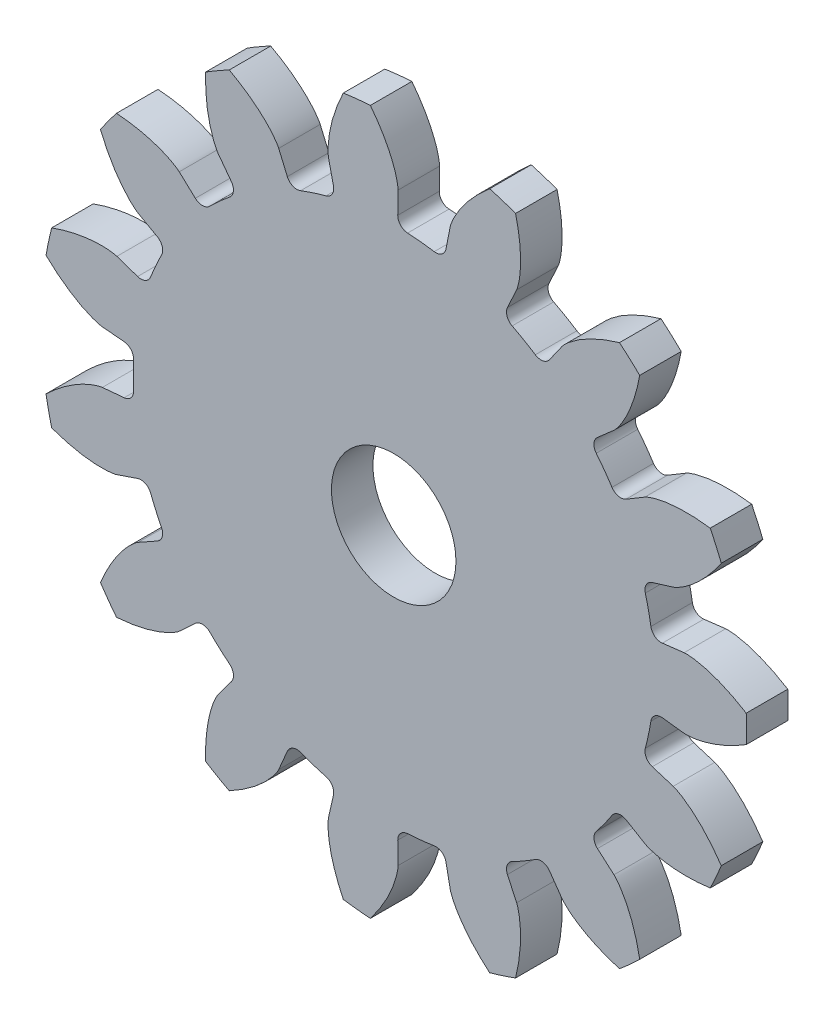
SolidWorks part; units mm, degrees
ref_plane "Front Plane" through (0, 0, 0) normal (0, 0, 1) x (1, 0, 0)
ref_plane "Top Plane" through (0, 0, 0) normal (0, 1, 0) x (1, 0, 0)
ref_plane "Right Plane" through (0, 0, 0) normal (1, 0, 0) x (0, 0, -1)
sketch "Model" plane through (0, 0, 0) normal (0, 0, 1) x (1, 0, 0)
  line L0 (-40.3391, -19.555) -> (-39.3393, -19.2145)
  line L1 (-38.3886, -21.3499) -> (-39.3106, -21.865)
  line L2 (-37.3332, -24.5867) -> (-36.5584, -23.869)
  line L3 (-39.9867, -16.1687) -> (-41.0386, -16.2643)
  line L4 (-14.0541, -16.5569) -> (-13.0053, -16.6821)
  line L5 (-16.3857, -24.2745) -> (-17.1805, -23.5789)
  line L6 (-26.7899, -29.0938) -> (-26.8049, -28.0377)
  line L7 (-14.5401, -11.1567) -> (-13.5311, -10.8446)
  line L8 (-21.0756, -27.7899) -> (-21.5188, -26.8312)
  line L9 (-13.5311, -19.1554) -> (-14.5401, -18.8433)
  line L10 (-41.0386, -13.7357) -> (-39.9867, -13.8313)
  line L11 (-19.4945, -25.6625) -> (-18.8858, -26.5256)
  line L12 (-15.8066, -21.6879) -> (-14.8994, -22.2288)
  line L13 (-34.8213, -25.4331) -> (-35.4541, -26.2787)
  line L14 (-29.9016, -27.7123) -> (-30.1358, -28.7422)
  line L15 (-24.4802, -27.7934) -> (-24.2752, -28.8295)
  line L16 (-32.5406, -27.9608) -> (-32.1247, -26.9899)
  line L17 (-24.2752, -1.1705) -> (-24.4802, -2.2066)
  line L18 (-35.4541, -3.7213) -> (-34.8213, -4.5669)
  line L19 (-39.3106, -8.135) -> (-38.3886, -8.6501)
  line L20 (-36.5584, -6.131) -> (-37.3332, -5.4133)
  line L21 (-17.1805, -6.4211) -> (-16.3857, -5.7255)
  line L22 (-32.1247, -3.0101) -> (-32.5406, -2.0392)
  line L23 (-30.1358, -1.2578) -> (-29.9016, -2.2877)
  line L24 (-39.3393, -10.7855) -> (-40.3391, -10.445)
  line L25 (-21.5188, -3.1688) -> (-21.0756, -2.2101)
  line L26 (-13.0053, -13.3179) -> (-14.0541, -13.4431)
  line L27 (-18.8858, -3.4744) -> (-19.4945, -4.3375)
  line L28 (-14.8994, -7.7712) -> (-15.8066, -8.3121)
  line L29 (-26.8049, -1.9623) -> (-26.7899, -0.9062)
  arc A0 (-38.7115, -19.5081) -> (-39.3393, -19.2145) centre (-39.1781, -19.6878) ccw
  arc A1 (-38.3886, -21.3499) -> (-38.1867, -20.6868) centre (-38.6324, -20.9134) ccw
  arc A2 (-38.7115, -19.5081) -> (-38.1867, -20.6868) centre (-27, -15) ccw
  arc A3 (-41.1288, -24.454) -> (-40.3573, -25.5158) centre (-27, -15) ccw
  arc A4 (-43.7526, -17.89) -> (-43.4797, -19.1738) centre (-27, -15) ccw
  arc A5 (-39.9867, -16.1687) -> (-39.5326, -15.6451) centre (-40.0319, -15.6708) ccw
  arc A6 (-14.0541, -16.5569) -> (-14.6071, -16.9747) centre (-14.1134, -17.0534) ccw
  arc A7 (-14.8754, -18.2367) -> (-14.6071, -16.9747) centre (-27, -15) ccw
  arc A8 (-11.7482, -22.5089) -> (-11.2144, -21.3099) centre (-27, -15) ccw
  arc A9 (-31.4863, -26.7199) -> (-32.1247, -26.9899) centre (-31.6651, -27.1868) ccw
  arc A10 (-17.2401, -22.8884) -> (-17.1805, -23.5789) centre (-16.8512, -23.2027) ccw
  arc A11 (-36.062, -29.3833) -> (-34.9254, -30.0396) centre (-27, -15) ccw
  arc A12 (-15.8066, -21.6879) -> (-16.4817, -21.8446) centre (-16.0626, -22.1173) ccw
  arc A13 (-14.8754, -18.2367) -> (-14.5401, -18.8433) centre (-14.3923, -18.3656) ccw
  arc A14 (-10.0127, -15.6562) -> (-10.0127, -14.3438) centre (-27, -15) ccw
  arc A15 (-24.4802, -27.7934) -> (-25.0484, -27.3965) centre (-24.9707, -27.8904) ccw
  arc A16 (-39.5326, -14.3549) -> (-39.5326, -15.6451) centre (-27, -15) ccw
  arc A17 (-14.6071, -13.0253) -> (-14.0541, -13.4431) centre (-14.1134, -12.9466) ccw
  arc A18 (-14.6071, -13.0253) -> (-14.8754, -11.7633) centre (-27, -15) ccw
  arc A19 (-22.3747, -31.3587) -> (-21.1265, -30.9531) centre (-27, -15) ccw
  arc A20 (-29.9016, -27.7123) -> (-30.2593, -27.1186) centre (-30.3891, -27.6014) ccw
  arc A21 (-26.3315, -27.5314) -> (-26.8049, -28.0377) centre (-26.3049, -28.0307) ccw
  arc A22 (-35.8653, -23.8819) -> (-34.9066, -24.7452) centre (-27, -15) ccw
  arc A23 (-34.8213, -25.4331) -> (-34.9066, -24.7452) centre (-35.2216, -25.1335) ccw
  arc A24 (-21.2924, -26.1761) -> (-21.5188, -26.8312) centre (-21.065, -26.6214) ccw
  arc A25 (-31.4863, -26.7199) -> (-30.2593, -27.1186) centre (-27, -15) ccw
  arc A26 (-19.4945, -25.6625) -> (-20.175, -25.531) centre (-19.9031, -25.9506) ccw
  arc A27 (-21.2924, -26.1761) -> (-20.175, -25.531) centre (-27, -15) ccw
  arc A28 (-17.2401, -22.8884) -> (-16.4817, -21.8446) centre (-27, -15) ccw
  circle A29 centre (-27, -15) radius 3
  arc A30 (-35.8653, -23.8819) -> (-36.5584, -23.869) centre (-36.2186, -24.2358) ccw
  arc A31 (-29.4283, -31.8257) -> (-28.123, -31.9629) centre (-27, -15) ccw
  arc A32 (-16.1209, -28.0631) -> (-15.1456, -27.1849) centre (-27, -15) ccw
  arc A33 (-26.3315, -27.5314) -> (-25.0484, -27.3965) centre (-27, -15) ccw
  arc A34 (-39.5326, -14.3549) -> (-39.9867, -13.8313) centre (-40.0319, -14.3292) ccw
  arc A35 (-34.9066, -5.2548) -> (-35.8653, -6.1181) centre (-27, -15) ccw
  arc A36 (-17.1805, -6.4211) -> (-17.2401, -7.1116) centre (-16.8512, -6.7973) ccw
  arc A37 (-32.1247, -3.0101) -> (-31.4863, -3.2801) centre (-31.6651, -2.8132) ccw
  arc A38 (-34.9254, 0.0396) -> (-36.062, -0.6167) centre (-27, -15) ccw
  arc A39 (-21.5188, -3.1688) -> (-21.2924, -3.8239) centre (-21.065, -3.3786) ccw
  arc A40 (-20.175, -4.469) -> (-19.4945, -4.3375) centre (-19.9031, -4.0494) ccw
  arc A41 (-25.0484, -2.6035) -> (-26.3315, -2.4686) centre (-27, -15) ccw
  arc A42 (-30.2593, -2.8814) -> (-29.9016, -2.2877) centre (-30.3891, -2.3986) ccw
  arc A43 (-38.1867, -9.3132) -> (-38.3886, -8.6501) centre (-38.6324, -9.0866) ccw
  arc A44 (-11.2144, -8.6901) -> (-11.7482, -7.4911) centre (-27, -15) ccw
  arc A45 (-34.9066, -5.2548) -> (-34.8213, -4.5669) centre (-35.2216, -4.8665) ccw
  arc A46 (-36.5584, -6.131) -> (-35.8653, -6.1181) centre (-36.2186, -5.7642) ccw
  arc A47 (-25.0484, -2.6035) -> (-24.4802, -2.2066) centre (-24.9707, -2.1096) ccw
  arc A48 (-16.4817, -8.1554) -> (-15.8066, -8.3121) centre (-16.0626, -7.8827) ccw
  arc A49 (-21.1265, 0.9531) -> (-22.3747, 1.3587) centre (-27, -15) ccw
  arc A50 (-26.8049, -1.9623) -> (-26.3315, -2.4686) centre (-26.3049, -1.9693) ccw
  arc A51 (-16.4817, -8.1554) -> (-17.2401, -7.1116) centre (-27, -15) ccw
  arc A52 (-30.2593, -2.8814) -> (-31.4863, -3.2801) centre (-27, -15) ccw
  arc A53 (-38.1867, -9.3132) -> (-38.7115, -10.4919) centre (-27, -15) ccw
  arc A54 (-39.3393, -10.7855) -> (-38.7115, -10.4919) centre (-39.1781, -10.3122) ccw
  arc A55 (-40.3573, -4.4842) -> (-41.1288, -5.546) centre (-27, -15) ccw
  arc A56 (-20.175, -4.469) -> (-21.2924, -3.8239) centre (-27, -15) ccw
  arc A57 (-14.5401, -11.1567) -> (-14.8754, -11.7633) centre (-14.3923, -11.6344) ccw
  arc A58 (-15.1456, -2.8151) -> (-16.1209, -1.9369) centre (-27, -15) ccw
  arc A59 (-28.123, 1.9629) -> (-29.4283, 1.8257) centre (-27, -15) ccw
  arc A60 (-43.4797, -10.8262) -> (-43.7526, -12.11) centre (-27, -15) ccw
  spline S0 degree 5 poles (-39.3106, -21.865) (-39.3407, -21.8818) (-39.3769, -21.9048) (-39.4387, -21.9509) (-39.5044, -22.0069) (-39.5963, -22.0861) (-39.6671, -22.1506) (-39.754, -22.2371) (-39.8267, -22.3139) (-39.91, -22.4056) (-40.0032, -22.5132) (-40.1157, -22.6528) (-40.2248, -22.7968) (-40.3507, -22.9756) (-40.4864, -23.1837) (-40.6113, -23.3905) (-40.7305, -23.6032) (-40.8483, -23.8302) (-40.9519, -24.0455) (-41.0271, -24.2124) (-41.0805, -24.3371) (-41.114, -24.4179) (-41.1288, -24.454) knots 0 0 0 0 0 0 0.057143 0.071429 0.128571 0.142857 0.2 0.214286 0.271429 0.3 0.342857 0.428571 0.5 0.557143 0.642857 0.728571 0.8 0.871429 0.942857 1 1 1 1 1 1
  spline S1 degree 5 poles (-43.4797, -19.1738) (-43.3605, -19.2166) (-43.2046, -19.2697) (-43.0027, -19.3335) (-42.755, -19.4037) (-42.4711, -19.4722) (-42.2609, -19.517) (-42.0513, -19.5552) (-41.8514, -19.5855) (-41.6795, -19.6064) (-41.5083, -19.6222) (-41.3648, -19.6317) (-41.2308, -19.6373) (-41.1153, -19.6389) (-40.9916, -19.6376) (-40.8948, -19.6347) (-40.79, -19.6285) (-40.7033, -19.6201) (-40.6086, -19.6085) (-40.5229, -19.5972) (-40.4466, -19.5848) (-40.3965, -19.5732) (-40.3554, -19.5606) (-40.3391, -19.555) knots -1 -1 -1 -1 -1 -1 -0.814286 -0.757143 -0.685714 -0.614286 -0.557143 -0.485714 -0.428571 -0.371429 -0.342857 -0.285714 -0.257143 -0.214286 -0.185714 -0.142857 -0.128571 -0.085714 -0.071429 -0.028571 0 0 0 0 0 0
  spline S2 degree 5 poles (-28.123, -31.9629) (-28.0454, -31.8628) (-27.9467, -31.7309) (-27.8237, -31.5586) (-27.6804, -31.3447) (-27.5275, -31.0959) (-27.4199, -30.9099) (-27.3188, -30.7223) (-27.2283, -30.5415) (-27.1553, -30.3845) (-27.0873, -30.2265) (-27.0339, -30.093) (-26.9873, -29.9673) (-26.9501, -29.858) (-26.913, -29.7399) (-26.8859, -29.647) (-26.8594, -29.5453) (-26.8406, -29.4603) (-26.8223, -29.3666) (-26.8066, -29.2816) (-26.7948, -29.2052) (-26.7903, -29.154) (-26.7897, -29.111) (-26.7899, -29.0938) knots -1 -1 -1 -1 -1 -1 -0.814286 -0.757143 -0.685714 -0.614286 -0.557143 -0.485714 -0.428571 -0.371429 -0.342857 -0.285714 -0.257143 -0.214286 -0.185714 -0.142857 -0.128571 -0.085714 -0.071429 -0.028571 0 0 0 0 0 0
  spline S3 degree 5 poles (-21.1265, -30.9531) (-21.0964, -30.8301) (-21.0598, -30.6695) (-21.0175, -30.462) (-20.9736, -30.2084) (-20.9351, -29.9189) (-20.9125, -29.7052) (-20.8964, -29.4927) (-20.8873, -29.2908) (-20.8844, -29.1176) (-20.8866, -28.9456) (-20.8921, -28.8019) (-20.9006, -28.6681) (-20.9111, -28.5531) (-20.9253, -28.4302) (-20.9383, -28.3343) (-20.9554, -28.2306) (-20.9729, -28.1453) (-20.9943, -28.0523) (-21.0145, -27.9683) (-21.0348, -27.8936) (-21.0515, -27.845) (-21.0684, -27.8055) (-21.0756, -27.7899) knots -1 -1 -1 -1 -1 -1 -0.814286 -0.757143 -0.685714 -0.614286 -0.557143 -0.485714 -0.428571 -0.371429 -0.342857 -0.285714 -0.257143 -0.214286 -0.185714 -0.142857 -0.128571 -0.085714 -0.071429 -0.028571 0 0 0 0 0 0
  spline S4 degree 5 poles (-40.3573, -25.5158) (-40.231, -25.5065) (-40.067, -25.4916) (-39.8566, -25.4678) (-39.6018, -25.4311) (-39.3146, -25.3783) (-39.1043, -25.3337) (-38.8972, -25.2833) (-38.7024, -25.2297) (-38.5368, -25.1788) (-38.3739, -25.1237) (-38.239, -25.074) (-38.1143, -25.0246) (-38.0082, -24.979) (-37.8957, -24.9275) (-37.8085, -24.8856) (-37.7152, -24.8372) (-37.6395, -24.7943) (-37.5576, -24.7452) (-37.4839, -24.7) (-37.4192, -24.6576) (-37.3782, -24.6267) (-37.3458, -24.5984) (-37.3332, -24.5867) knots -1 -1 -1 -1 -1 -1 -0.814286 -0.757143 -0.685714 -0.614286 -0.557143 -0.485714 -0.428571 -0.371429 -0.342857 -0.285714 -0.257143 -0.214286 -0.185714 -0.142857 -0.128571 -0.085714 -0.071429 -0.028571 0 0 0 0 0 0
  spline S5 degree 5 poles (-10.0127, -14.3438) (-10.1203, -14.2771) (-10.2618, -14.1927) (-10.446, -14.0883) (-10.6737, -13.9682) (-10.9371, -13.8421) (-11.1334, -13.7546) (-11.3305, -13.6736) (-11.5197, -13.6025) (-11.6836, -13.5463) (-11.8477, -13.4952) (-11.9862, -13.4561) (-12.116, -13.4228) (-12.2287, -13.3972) (-12.3499, -13.3728) (-12.4452, -13.3555) (-12.549, -13.3397) (-12.6356, -13.33) (-12.7306, -13.3216) (-12.8168, -13.3148) (-12.8941, -13.3111) (-12.9455, -13.312) (-12.9882, -13.3158) (-13.0053, -13.3179) knots -1 -1 -1 -1 -1 -1 -0.814286 -0.757143 -0.685714 -0.614286 -0.557143 -0.485714 -0.428571 -0.371429 -0.342857 -0.285714 -0.257143 -0.214286 -0.185714 -0.142857 -0.128571 -0.085714 -0.071429 -0.028571 0 0 0 0 0 0
  spline S6 degree 5 poles (-15.1456, -27.1849) (-15.1681, -27.0603) (-15.2, -26.8987) (-15.2457, -26.692) (-15.3088, -26.4424) (-15.3913, -26.1623) (-15.4577, -25.9578) (-15.5294, -25.7572) (-15.6032, -25.569) (-15.671, -25.4096) (-15.7429, -25.2534) (-15.8064, -25.1244) (-15.8686, -25.0056) (-15.925, -24.9048) (-15.9879, -24.7983) (-16.0388, -24.7159) (-16.0966, -24.6282) (-16.1473, -24.5574) (-16.2046, -24.4811) (-16.2573, -24.4126) (-16.3062, -24.3527) (-16.3412, -24.315) (-16.3727, -24.2858) (-16.3857, -24.2745) knots -1 -1 -1 -1 -1 -1 -0.814286 -0.757143 -0.685714 -0.614286 -0.557143 -0.485714 -0.428571 -0.371429 -0.342857 -0.285714 -0.257143 -0.214286 -0.185714 -0.142857 -0.128571 -0.085714 -0.071429 -0.028571 0 0 0 0 0 0
  spline S7 degree 5 poles (-35.4541, -26.2787) (-35.4747, -26.3062) (-35.4984, -26.342) (-35.5362, -26.4093) (-35.5733, -26.4871) (-35.6252, -26.5969) (-35.6636, -26.6846) (-35.7078, -26.799) (-35.743, -26.8987) (-35.7818, -27.0163) (-35.8232, -27.1525) (-35.8691, -27.3258) (-35.9103, -27.5017) (-35.9525, -27.7163) (-35.9919, -27.9616) (-36.0218, -28.2013) (-36.0442, -28.4441) (-36.0594, -28.6994) (-36.0666, -28.9382) (-36.0674, -29.1213) (-36.0655, -29.2569) (-36.0632, -29.3444) (-36.062, -29.3833) knots 0 0 0 0 0 0 0.057143 0.071429 0.128571 0.142857 0.2 0.214286 0.271429 0.3 0.342857 0.428571 0.5 0.557143 0.642857 0.728571 0.8 0.871429 0.942857 1 1 1 1 1 1
  spline S8 degree 5 poles (-43.7526, -12.11) (-43.6611, -12.1977) (-43.5403, -12.3096) (-43.3818, -12.45) (-43.1841, -12.6148) (-42.9526, -12.7929) (-42.7788, -12.9193) (-42.6028, -13.0395) (-42.4325, -13.1484) (-42.284, -13.2375) (-42.134, -13.3216) (-42.0067, -13.3886) (-41.8866, -13.4482) (-41.7818, -13.4966) (-41.6682, -13.5458) (-41.5787, -13.5825) (-41.4804, -13.6195) (-41.3977, -13.647) (-41.3065, -13.675) (-41.2236, -13.6995) (-41.1488, -13.7192) (-41.0984, -13.729) (-41.0557, -13.7342) (-41.0386, -13.7357) knots -1 -1 -1 -1 -1 -1 -0.814286 -0.757143 -0.685714 -0.614286 -0.557143 -0.485714 -0.428571 -0.371429 -0.342857 -0.285714 -0.257143 -0.214286 -0.185714 -0.142857 -0.128571 -0.085714 -0.071429 -0.028571 0 0 0 0 0 0
  spline S9 degree 5 poles (-30.1358, -28.7422) (-30.1434, -28.7758) (-30.1505, -28.8181) (-30.1576, -28.8949) (-30.1599, -28.9811) (-30.1626, -29.1024) (-30.162, -29.1982) (-30.1559, -29.3207) (-30.1475, -29.4261) (-30.1351, -29.5493) (-30.1175, -29.6906) (-30.0889, -29.8676) (-30.055, -30.045) (-30.0064, -30.2583) (-29.9425, -30.4983) (-29.8724, -30.7295) (-29.7941, -30.9605) (-29.7041, -31.1998) (-29.6136, -31.4209) (-29.5398, -31.5884) (-29.4829, -31.7116) (-29.4452, -31.7906) (-29.4283, -31.8257) knots 0 0 0 0 0 0 0.057143 0.071429 0.128571 0.142857 0.2 0.214286 0.271429 0.3 0.342857 0.428571 0.5 0.557143 0.642857 0.728571 0.8 0.871429 0.942857 1 1 1 1 1 1
  spline S10 degree 5 poles (-24.2752, -28.8295) (-24.2685, -28.8633) (-24.2578, -28.9048) (-24.2331, -28.9779) (-24.2001, -29.0576) (-24.1532, -29.1696) (-24.1137, -29.2568) (-24.0583, -29.3662) (-24.0077, -29.4591) (-23.9463, -29.5666) (-23.8728, -29.6885) (-23.7747, -29.8386) (-23.6715, -29.9869) (-23.5404, -30.1619) (-23.3844, -30.3553) (-23.2263, -30.5379) (-23.0608, -30.7171) (-22.8813, -30.8992) (-22.7086, -31.0643) (-22.5731, -31.1873) (-22.471, -31.2767) (-22.4045, -31.3335) (-22.3747, -31.3587) knots 0 0 0 0 0 0 0.057143 0.071429 0.128571 0.142857 0.2 0.214286 0.271429 0.3 0.342857 0.428571 0.5 0.557143 0.642857 0.728571 0.8 0.871429 0.942857 1 1 1 1 1 1
  spline S11 degree 5 poles (-34.9254, -30.0396) (-34.8138, -29.9797) (-34.67, -29.8994) (-34.4874, -29.792) (-34.2696, -29.6549) (-34.0287, -29.4898) (-33.8547, -29.3636) (-33.6861, -29.2333) (-33.5299, -29.105) (-33.3993, -28.9913) (-33.2729, -28.8746) (-33.1699, -28.7743) (-33.0761, -28.6785) (-32.9976, -28.5937) (-32.9158, -28.5009) (-32.8532, -28.4271) (-32.7876, -28.345) (-32.7359, -28.275) (-32.6811, -28.1968) (-32.6322, -28.1256) (-32.5903, -28.0606) (-32.5654, -28.0156) (-32.5473, -27.9766) (-32.5406, -27.9608) knots -1 -1 -1 -1 -1 -1 -0.814286 -0.757143 -0.685714 -0.614286 -0.557143 -0.485714 -0.428571 -0.371429 -0.342857 -0.285714 -0.257143 -0.214286 -0.185714 -0.142857 -0.128571 -0.085714 -0.071429 -0.028571 0 0 0 0 0 0
  spline S12 degree 5 poles (-14.8994, -22.2288) (-14.8698, -22.2465) (-14.8318, -22.2663) (-14.7609, -22.2968) (-14.6796, -22.3256) (-14.5651, -22.3657) (-14.4738, -22.3948) (-14.3554, -22.4268) (-14.2526, -22.4513) (-14.1315, -22.4776) (-13.9918, -22.5045) (-13.8146, -22.5321) (-13.6354, -22.5547) (-13.4176, -22.5743) (-13.1695, -22.5878) (-12.928, -22.5925) (-12.6841, -22.5894) (-12.4287, -22.5778) (-12.1904, -22.56) (-12.0083, -22.5416) (-11.8736, -22.5255) (-11.7868, -22.5141) (-11.7482, -22.5089) knots 0 0 0 0 0 0 0.057143 0.071429 0.128571 0.142857 0.2 0.214286 0.271429 0.3 0.342857 0.428571 0.5 0.557143 0.642857 0.728571 0.8 0.871429 0.942857 1 1 1 1 1 1
  spline S13 degree 5 poles (-11.2144, -21.3099) (-11.2856, -21.2051) (-11.3805, -21.0705) (-11.5064, -20.9002) (-11.6655, -20.6979) (-11.8549, -20.4756) (-11.9986, -20.3158) (-12.1458, -20.1617) (-12.2897, -20.0197) (-12.4165, -19.9017) (-12.5457, -19.7883) (-12.6562, -19.6962) (-12.7613, -19.613) (-12.8538, -19.5439) (-12.9546, -19.4722) (-13.0346, -19.4176) (-13.1231, -19.361) (-13.1982, -19.3169) (-13.2816, -19.2706) (-13.3576, -19.2294) (-13.4266, -19.1945) (-13.474, -19.1744) (-13.5146, -19.1605) (-13.5311, -19.1554) knots -1 -1 -1 -1 -1 -1 -0.814286 -0.757143 -0.685714 -0.614286 -0.557143 -0.485714 -0.428571 -0.371429 -0.342857 -0.285714 -0.257143 -0.214286 -0.185714 -0.142857 -0.128571 -0.085714 -0.071429 -0.028571 0 0 0 0 0 0
  spline S14 degree 5 poles (-41.0386, -16.2643) (-41.0729, -16.2674) (-41.1153, -16.2737) (-41.1906, -16.2907) (-41.2733, -16.3152) (-41.3895, -16.3501) (-41.4804, -16.3802) (-41.595, -16.4239) (-41.6926, -16.4645) (-41.806, -16.5144) (-41.9349, -16.5747) (-42.0945, -16.6566) (-42.2527, -16.7437) (-42.4405, -16.8558) (-42.6491, -16.9907) (-42.8473, -17.1289) (-43.0427, -17.2747) (-43.2426, -17.4342) (-43.4249, -17.5887) (-43.5614, -17.7106) (-43.6609, -17.8028) (-43.7244, -17.863) (-43.7526, -17.89) knots 0 0 0 0 0 0 0.057143 0.071429 0.128571 0.142857 0.2 0.214286 0.271429 0.3 0.342857 0.428571 0.5 0.557143 0.642857 0.728571 0.8 0.871429 0.942857 1 1 1 1 1 1
  spline S15 degree 5 poles (-18.8858, -26.5256) (-18.866, -26.5538) (-18.8393, -26.5873) (-18.7869, -26.644) (-18.7244, -26.7035) (-18.636, -26.7866) (-18.5645, -26.8503) (-18.4693, -26.9277) (-18.3854, -26.9919) (-18.2855, -27.0652) (-18.1688, -27.1466) (-18.0181, -27.2439) (-17.8636, -27.3374) (-17.6726, -27.4439) (-17.4514, -27.5571) (-17.2327, -27.6597) (-17.0087, -27.756) (-16.7706, -27.8494) (-16.5457, -27.93) (-16.3719, -27.9873) (-16.2423, -28.0274) (-16.1584, -28.0523) (-16.1209, -28.0631) knots 0 0 0 0 0 0 0.057143 0.071429 0.128571 0.142857 0.2 0.214286 0.271429 0.3 0.342857 0.428571 0.5 0.557143 0.642857 0.728571 0.8 0.871429 0.942857 1 1 1 1 1 1
  spline S16 degree 5 poles (-36.062, -0.6167) (-36.0659, -0.7432) (-36.0682, -0.9079) (-36.0665, -1.1197) (-36.0567, -1.3769) (-36.0342, -1.6681) (-36.0119, -1.8818) (-35.9834, -2.093) (-35.9504, -2.2924) (-35.9172, -2.4625) (-35.8793, -2.6302) (-35.844, -2.7696) (-35.8079, -2.8987) (-35.7737, -3.009) (-35.7343, -3.1263) (-35.7016, -3.2174) (-35.6633, -3.3152) (-35.6285, -3.395) (-35.5882, -3.4816) (-35.551, -3.5596) (-35.5156, -3.6283) (-35.4891, -3.6724) (-35.4644, -3.7075) (-35.4541, -3.7213) knots -1 -1 -1 -1 -1 -1 -0.814286 -0.757143 -0.685714 -0.614286 -0.557143 -0.485714 -0.428571 -0.371429 -0.342857 -0.285714 -0.257143 -0.214286 -0.185714 -0.142857 -0.128571 -0.085714 -0.071429 -0.028571 0 0 0 0 0 0
  spline S17 degree 5 poles (-11.7482, -7.4911) (-11.8737, -7.474) (-12.0373, -7.4544) (-12.248, -7.434) (-12.5048, -7.4169) (-12.7968, -7.4088) (-13.0117, -7.4087) (-13.2247, -7.415) (-13.4265, -7.4269) (-13.599, -7.4422) (-13.7698, -7.4623) (-13.9121, -7.4829) (-14.0443, -7.5053) (-14.1576, -7.5278) (-14.2784, -7.5547) (-14.3724, -7.5777) (-14.4737, -7.6055) (-14.5567, -7.6318) (-14.647, -7.6628) (-14.7284, -7.6917) (-14.8005, -7.7197) (-14.8471, -7.7414) (-14.8846, -7.7623) (-14.8994, -7.7712) knots -1 -1 -1 -1 -1 -1 -0.814286 -0.757143 -0.685714 -0.614286 -0.557143 -0.485714 -0.428571 -0.371429 -0.342857 -0.285714 -0.257143 -0.214286 -0.185714 -0.142857 -0.128571 -0.085714 -0.071429 -0.028571 0 0 0 0 0 0
  spline S18 degree 5 poles (-26.7899, -0.9062) (-26.7894, -0.8717) (-26.7913, -0.8289) (-26.8003, -0.7523) (-26.816, -0.6674) (-26.8386, -0.5482) (-26.859, -0.4546) (-26.8905, -0.3361) (-26.9207, -0.2348) (-26.9584, -0.1168) (-27.005, 0.0177) (-27.0697, 0.1849) (-27.1398, 0.3514) (-27.2317, 0.5499) (-27.3441, 0.7714) (-27.4608, 0.983) (-27.5853, 1.1926) (-27.7231, 1.4081) (-27.8576, 1.6055) (-27.9646, 1.754) (-28.0459, 1.8626) (-28.0992, 1.9321) (-28.123, 1.9629) knots 0 0 0 0 0 0 0.057143 0.071429 0.128571 0.142857 0.2 0.214286 0.271429 0.3 0.342857 0.428571 0.5 0.557143 0.642857 0.728571 0.8 0.871429 0.942857 1 1 1 1 1 1
  spline S19 degree 5 poles (-13.0053, -16.6821) (-12.9711, -16.6862) (-12.9283, -16.6888) (-12.8512, -16.6879) (-12.7652, -16.6812) (-12.6442, -16.6712) (-12.549, -16.6606) (-12.4279, -16.6417) (-12.324, -16.6223) (-12.2027, -16.5971) (-12.0641, -16.5648) (-11.891, -16.5179) (-11.7181, -16.4657) (-11.5111, -16.395) (-11.279, -16.3064) (-11.0564, -16.2125) (-10.8349, -16.1105) (-10.6062, -15.996) (-10.3959, -15.8828) (-10.2369, -15.7919) (-10.1204, -15.7225) (-10.0458, -15.6768) (-10.0127, -15.6562) knots 0 0 0 0 0 0 0.057143 0.071429 0.128571 0.142857 0.2 0.214286 0.271429 0.3 0.342857 0.428571 0.5 0.557143 0.642857 0.728571 0.8 0.871429 0.942857 1 1 1 1 1 1
  spline S20 degree 5 poles (-22.3747, 1.3587) (-22.4714, 1.2769) (-22.5954, 1.1684) (-22.7516, 1.0255) (-22.9362, 0.8461) (-23.1375, 0.6345) (-23.2814, 0.4749) (-23.4193, 0.3124) (-23.5454, 0.1544) (-23.6495, 0.016) (-23.7488, -0.1243) (-23.8288, -0.2439) (-23.9006, -0.3571) (-23.9597, -0.4563) (-24.0205, -0.5641) (-24.0664, -0.6494) (-24.1134, -0.7433) (-24.1494, -0.8226) (-24.1868, -0.9104) (-24.2198, -0.9902) (-24.2473, -1.0625) (-24.2623, -1.1117) (-24.2719, -1.1536) (-24.2752, -1.1705) knots -1 -1 -1 -1 -1 -1 -0.814286 -0.757143 -0.685714 -0.614286 -0.557143 -0.485714 -0.428571 -0.371429 -0.342857 -0.285714 -0.257143 -0.214286 -0.185714 -0.142857 -0.128571 -0.085714 -0.071429 -0.028571 0 0 0 0 0 0
  spline S21 degree 5 poles (-29.4283, 1.8257) (-29.4834, 1.7116) (-29.5525, 1.5621) (-29.6371, 1.368) (-29.7327, 1.129) (-29.8306, 0.8539) (-29.8971, 0.6495) (-29.957, 0.445) (-30.008, 0.2494) (-30.0467, 0.0806) (-30.0804, -0.088) (-30.1048, -0.2298) (-30.1243, -0.3624) (-30.138, -0.4771) (-30.1497, -0.6003) (-30.1569, -0.6968) (-30.1617, -0.8018) (-30.1624, -0.8888) (-30.1608, -0.9842) (-30.1585, -1.0706) (-30.1541, -1.1479) (-30.1479, -1.1989) (-30.1396, -1.241) (-30.1358, -1.2578) knots -1 -1 -1 -1 -1 -1 -0.814286 -0.757143 -0.685714 -0.614286 -0.557143 -0.485714 -0.428571 -0.371429 -0.342857 -0.285714 -0.257143 -0.214286 -0.185714 -0.142857 -0.128571 -0.085714 -0.071429 -0.028571 0 0 0 0 0 0
  spline S22 degree 5 poles (-41.1288, -5.546) (-41.0809, -5.6632) (-41.016, -5.8147) (-40.9283, -6.0074) (-40.8147, -6.2384) (-40.6757, -6.4952) (-40.5684, -6.6814) (-40.4565, -6.8628) (-40.3452, -7.0315) (-40.2457, -7.1733) (-40.1429, -7.3111) (-40.0539, -7.4241) (-39.9684, -7.5274) (-39.8923, -7.6143) (-39.8086, -7.7054) (-39.7417, -7.7753) (-39.667, -7.8491) (-39.6027, -7.9079) (-39.5307, -7.9705) (-39.465, -8.0266) (-39.4047, -8.0751) (-39.3626, -8.1046) (-39.3257, -8.1266) (-39.3106, -8.135) knots -1 -1 -1 -1 -1 -1 -0.814286 -0.757143 -0.685714 -0.614286 -0.557143 -0.485714 -0.428571 -0.371429 -0.342857 -0.285714 -0.257143 -0.214286 -0.185714 -0.142857 -0.128571 -0.085714 -0.071429 -0.028571 0 0 0 0 0 0
  spline S23 degree 5 poles (-32.5406, -2.0392) (-32.5541, -2.0075) (-32.5733, -1.9692) (-32.6126, -1.9028) (-32.6615, -1.8317) (-32.7306, -1.732) (-32.7874, -1.6548) (-32.8643, -1.5593) (-32.9331, -1.479) (-33.0156, -1.3866) (-33.1128, -1.2827) (-33.2399, -1.1562) (-33.3717, -1.0326) (-33.5364, -0.8887) (-33.7291, -0.732) (-33.9218, -0.5862) (-34.1209, -0.4454) (-34.3343, -0.3046) (-34.5375, -0.179) (-34.6957, -0.0868) (-34.8141, -0.0206) (-34.891, 0.0211) (-34.9254, 0.0396) knots 0 0 0 0 0 0 0.057143 0.071429 0.128571 0.142857 0.2 0.214286 0.271429 0.3 0.342857 0.428571 0.5 0.557143 0.642857 0.728571 0.8 0.871429 0.942857 1 1 1 1 1 1
  spline S24 degree 5 poles (-37.3332, -5.4133) (-37.3585, -5.3899) (-37.3916, -5.3626) (-37.4545, -5.318) (-37.5281, -5.2729) (-37.6318, -5.2099) (-37.715, -5.1625) (-37.8242, -5.1066) (-37.9196, -5.0612) (-38.0326, -5.0103) (-38.1636, -4.9549) (-38.3312, -4.8911) (-38.5018, -4.8318) (-38.7108, -4.7673) (-38.9507, -4.7025) (-39.186, -4.6477) (-39.4251, -4.6) (-39.6774, -4.5582) (-39.9141, -4.5261) (-40.0961, -4.5062) (-40.2312, -4.494) (-40.3185, -4.4871) (-40.3573, -4.4842) knots 0 0 0 0 0 0 0.057143 0.071429 0.128571 0.142857 0.2 0.214286 0.271429 0.3 0.342857 0.428571 0.5 0.557143 0.642857 0.728571 0.8 0.871429 0.942857 1 1 1 1 1 1
  spline S25 degree 5 poles (-40.3391, -10.445) (-40.3717, -10.4339) (-40.413, -10.4224) (-40.4887, -10.4073) (-40.5742, -10.396) (-40.6946, -10.3806) (-40.7899, -10.3712) (-40.9124, -10.3645) (-41.018, -10.3618) (-41.1419, -10.3613) (-41.2842, -10.364) (-41.4633, -10.3739) (-41.6433, -10.3891) (-41.8604, -10.4152) (-42.1059, -10.4536) (-42.3431, -10.4992) (-42.581, -10.5529) (-42.8284, -10.6173) (-43.0578, -10.6843) (-43.2321, -10.7401) (-43.3605, -10.7839) (-43.443, -10.8131) (-43.4797, -10.8262) knots 0 0 0 0 0 0 0.057143 0.071429 0.128571 0.142857 0.2 0.214286 0.271429 0.3 0.342857 0.428571 0.5 0.557143 0.642857 0.728571 0.8 0.871429 0.942857 1 1 1 1 1 1
  spline S26 degree 5 poles (-16.3857, -5.7255) (-16.3598, -5.7028) (-16.3292, -5.6728) (-16.2783, -5.6148) (-16.2257, -5.5464) (-16.1522, -5.4498) (-16.0964, -5.372) (-16.0293, -5.2693) (-15.9742, -5.1791) (-15.9118, -5.0721) (-15.843, -4.9475) (-15.762, -4.7875) (-15.6852, -4.624) (-15.5992, -4.4229) (-15.5097, -4.1912) (-15.4306, -3.9629) (-15.3582, -3.73) (-15.2903, -3.4835) (-15.2336, -3.2514) (-15.1948, -3.0725) (-15.1685, -2.9395) (-15.1525, -2.8534) (-15.1456, -2.8151) knots 0 0 0 0 0 0 0.057143 0.071429 0.128571 0.142857 0.2 0.214286 0.271429 0.3 0.342857 0.428571 0.5 0.557143 0.642857 0.728571 0.8 0.871429 0.942857 1 1 1 1 1 1
  spline S27 degree 5 poles (-21.0756, -2.2101) (-21.0612, -2.1788) (-21.0454, -2.1389) (-21.0225, -2.0653) (-21.0023, -1.9814) (-20.9744, -1.8633) (-20.9551, -1.7695) (-20.9356, -1.6484) (-20.922, -1.5436) (-20.9085, -1.4204) (-20.8963, -1.2786) (-20.8874, -1.0995) (-20.8837, -0.9189) (-20.887, -0.7002) (-20.8995, -0.4521) (-20.9201, -0.2114) (-20.9486, 0.0308) (-20.9868, 0.2836) (-21.0294, 0.5187) (-21.0667, 0.6979) (-21.0968, 0.8302) (-21.1172, 0.9153) (-21.1265, 0.9531) knots 0 0 0 0 0 0 0.057143 0.071429 0.128571 0.142857 0.2 0.214286 0.271429 0.3 0.342857 0.428571 0.5 0.557143 0.642857 0.728571 0.8 0.871429 0.942857 1 1 1 1 1 1
  spline S28 degree 5 poles (-13.5311, -10.8446) (-13.4981, -10.8344) (-13.458, -10.8194) (-13.3879, -10.7871) (-13.312, -10.746) (-13.2056, -10.6877) (-13.123, -10.6393) (-13.02, -10.5727) (-12.9329, -10.5127) (-12.8324, -10.4404) (-12.7189, -10.3545) (-12.5798, -10.2413) (-12.4431, -10.1232) (-12.2828, -9.9745) (-12.1068, -9.7991) (-11.9417, -9.6228) (-11.7808, -9.4395) (-11.6185, -9.2419) (-11.4723, -9.053) (-11.3641, -8.9053) (-11.2859, -8.7945) (-11.2363, -8.7223) (-11.2144, -8.6901) knots 0 0 0 0 0 0 0.057143 0.071429 0.128571 0.142857 0.2 0.214286 0.271429 0.3 0.342857 0.428571 0.5 0.557143 0.642857 0.728571 0.8 0.871429 0.942857 1 1 1 1 1 1
  spline S29 degree 5 poles (-16.1209, -1.9369) (-16.2425, -1.9722) (-16.3999, -2.0209) (-16.6007, -2.088) (-16.8423, -2.1768) (-17.1123, -2.2882) (-17.3087, -2.3755) (-17.5008, -2.4678) (-17.6802, -2.5608) (-17.8316, -2.645) (-17.9794, -2.7328) (-18.1011, -2.8095) (-18.2128, -2.8837) (-18.3071, -2.9503) (-18.4065, -3.0241) (-18.483, -3.0833) (-18.5642, -3.1499) (-18.6294, -3.2077) (-18.6992, -3.2727) (-18.7619, -3.3322) (-18.8164, -3.3871) (-18.8501, -3.4259) (-18.8759, -3.4603) (-18.8858, -3.4744) knots -1 -1 -1 -1 -1 -1 -0.814286 -0.757143 -0.685714 -0.614286 -0.557143 -0.485714 -0.428571 -0.371429 -0.342857 -0.285714 -0.257143 -0.214286 -0.185714 -0.142857 -0.128571 -0.085714 -0.071429 -0.028571 0 0 0 0 0 0
extrude "Boss-Extrude1" add sketch "Model" along normal blind 2
